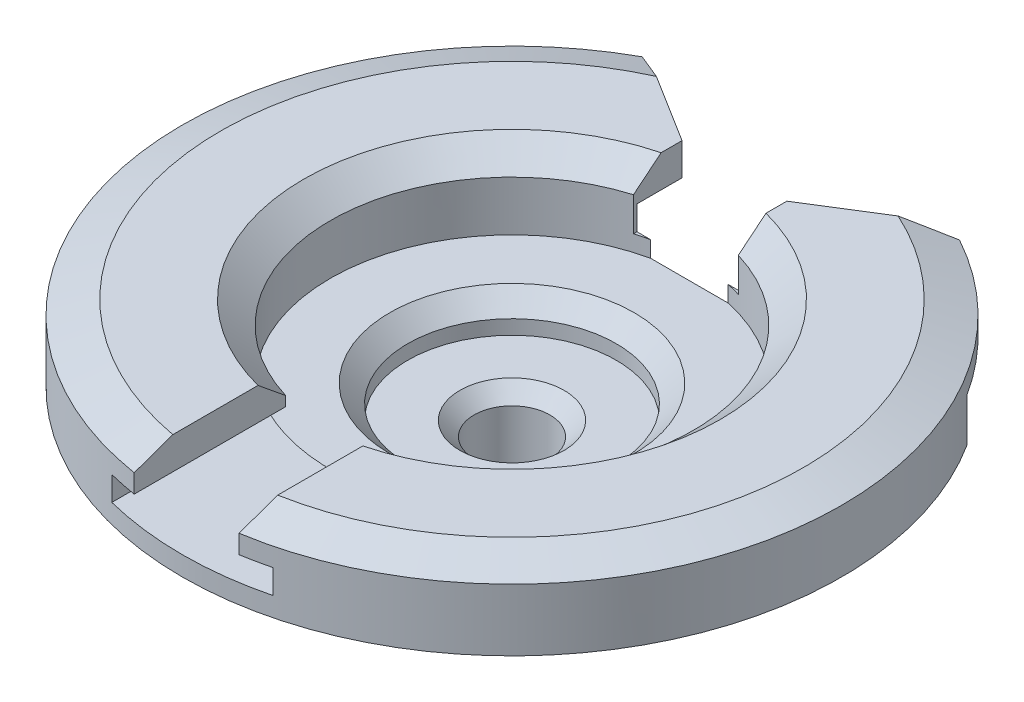
SolidWorks part; units mm, degrees
ref_plane "Alzado" through (0, 0, 0) normal (0, 0, 1) x (1, 0, 0)
ref_plane "Planta" through (0, 0, 0) normal (0, 1, 0) x (1, 0, 0)
ref_plane "Vista lateral" through (0, 0, 0) normal (1, 0, 0) x (0, 0, -1)
sketch "Sketch1" plane through (0, 0, 0) normal (0, 1, 0) x (1, 0, 0)
  circle A0 centre (0, 0) radius 1.25
  dimension "D1" = 2.5
extrude "Boss-Extrude1" add sketch "Sketch1" along normal blind 0.58
sketch "Sketch2" plane through (0, 0.58, 0) normal (0, 1, 0) x (1, 0, 0)
  circle A0 centre (0, 0) radius 2.043
  dimension "D1" = 4.086
extrude "Boss-Extrude2" add sketch "Sketch2" along normal blind 0.47
sketch "Sketch3" plane through (0, 0, 0) normal (0, 1, 0) x (1, 0, 0)
  circle A0 centre (0, 0) radius 0.6465
  dimension "D1" = 1.293
extrude "Cut-Extrude1" cut sketch "Sketch3" along normal up to next from offset 0.4
sketch "Sketch4" plane through (0, 0, 0) normal (0, 1, 0) x (1, 0, 0)
  circle A0 centre (0, 0) radius 1.126
  dimension "D1" = 2.252
extrude "Cut-Extrude2" cut sketch "Sketch4" along normal up to next from offset 0.6
sketch "Sketch5" plane through (0, 0, 0) normal (0, 1, 0) x (1, 0, 0)
  circle A0 centre (0, 0) radius 0.235
  dimension "D1" = 0.47
extrude "Cut-Extrude3" cut sketch "Sketch5" along normal up to next
chamfer "Chamfer1" distance 0.05 angle 45 1 edges at (0, 0, 1.25)
chamfer "Chamfer2" distance 0.088 angle 45 1 edges at (0, 0.4, 0.235)
chamfer "Chamfer3" distance 0.111 angle 45 1 edges at (0, 0.6, 0.6465)
chamfer "Chamfer4" distance 0.165 distance2 0.14 1 edges at (0, 1.05, 1.126)
chamfer "Chamfer5" distance 0.085 distance2 0.236 1 edges at (0, 1.05, 2.043)
sketch "Sketch7" plane through (0, 0, 0) normal (0, 0, 1) x (1, 0, 0)
  line L0 (-2.043, 0.58) -> (2.043, 0.58) construction
  line L1 (-2.043, 0.58) -> (2.043, 0.58) construction
  line L2 (0, -1000) -> (0, 49000) construction
  line L3 (-0.325, -999.994) -> (-0.325, 49000.006) construction
  line L4 (-0.5, -1000.0992) -> (-0.5, 48999.9008) construction
  line L5 (-1001.0813, 0.7) -> (48998.9187, 0.7) construction
  line L6 (-1001.0241, 0.85) -> (48998.9759, 0.85) construction
  line L7 (-0.325, 1.2203) -> (-0.325, 0.85)
  line L8 (-0.325, 0.85) -> (-0.5, 0.85)
  line L9 (-0.5, 0.85) -> (-0.5, 0.7)
  line L10 (-0.5, 0.7) -> (0.5, 0.7)
  line L11 (-0.325, 1.2203) -> (0.325, 1.2203)
  line L12 (0.5, 0.85) -> (0.5, 0.7)
  line L13 (0.325, 0.85) -> (0.5, 0.85)
  line L14 (0.325, 1.2203) -> (0.325, 0.85)
  point P20 (0, 0.7)
  point P23 (0, 1.2203)
  dimension "D1" = 0.5
  dimension "D2" = 0.325
  dimension "D3" = 0.12
  dimension "D4" = 0.15
extrude "Cut-Extrude4" cut sketch "Sketch7" along normal up to next
sketch "Sketch8" plane through (0, 0.6, 0) normal (0, 1, 0) x (1, 0, 0)
  line L0 (0, -1000) -> (0, 49000) construction
  line L1 (-0.24, -999.9108) -> (-0.24, 49000.0892) construction
  line L2 (0.24, -999.85) -> (0.24, 49000.15) construction
  line L4 (-0.24, 0.9343) -> (0.24, 0.9343)
  line L5 (-0.24, 0.9343) -> (-0.24, 2.6388)
  line L6 (-0.24, 2.6388) -> (0.24, 2.6388)
  line L7 (0.24, 0.9343) -> (0.24, 2.6388)
  dimension "D1" = 0.24
  dimension "D2" = 0.24
extrude "Cut-Extrude5" cut sketch "Sketch8" along normal up to next
sketch "Sketch9" plane through (0, 0.7, 0) normal (0, 1, 0) x (1, 0, 0)
  line L0 (0, -1000) -> (0, 49000) construction
  line L1 (0.325, -999.8269) -> (0.325, 49000.1731) construction
  line L2 (-0.325, -999.7009) -> (-0.325, 49000.2991) construction
  line L4 (-0.325, 2.2512) -> (0.325, 2.2512)
  line L5 (-0.325, 2.2512) -> (-0.325, 0.9579)
  line L6 (-0.325, 0.9579) -> (0.325, 0.9579)
  line L7 (0.325, 2.2512) -> (0.325, 0.9579)
  dimension "D1" = 0.325
  dimension "D2" = 0.325
extrude "Cut-Extrude6" cut sketch "Sketch9" along normal up to next
sketch "Sketch10" plane through (0, 0, 0) normal (0, 1, 0) x (1, 0, 0)
  line L0 (-1000, 0) -> (49000, 0) construction
  line L1 (-999.9255, 1.1) -> (49000.0745, 1.1) construction
  line L3 (-2.5511, 2.2979) -> (2.5423, 2.2979)
  line L4 (-2.5511, 2.2979) -> (-2.5511, 1.1)
  line L5 (-2.5511, 1.1) -> (2.5423, 1.1)
  line L6 (2.5423, 2.2979) -> (2.5423, 1.1)
  dimension "D1" = 1.1
extrude "Cut-Extrude7" cut sketch "Sketch10" along normal blind 0.85
sketch "Sketch11" plane through (0, 0, 0) normal (0, 1, 0) x (1, 0, 0)
  line L0 (-0.325, 2.017) -> (-0.325, 1.1) construction
  line L1 (-0.325, 2.017) -> (-0.325, 1.1) construction
  line L2 (0.325, 1.1) -> (0.325, 2.017) construction
  line L3 (0.325, 1.1) -> (0.325, 2.017) construction
  line L4 (-1000.2319, 1.379) -> (48999.7681, 1.379) construction
  line L5 (-0.325, 1.379) -> (-42402.7298, 26497.3422) construction
  line L6 (0.325, 1.379) -> (42402.7298, 26497.3422) construction
  line L7 (-1.8317, 2.3205) -> (0, 1.1759)
  line L8 (0, 1.1759) -> (1.8317, 2.3205)
  line L9 (1.8317, 2.3205) -> (-1.8317, 2.3205)
  point P5 (-0.325, 1.379)
  point P7 (0.325, 1.379)
  dimension "D1" = 0.279
  dimension "D2" = 58
  dimension "D3" = 58
extrude "Cut-Extrude8" cut sketch "Sketch11" along normal through all
